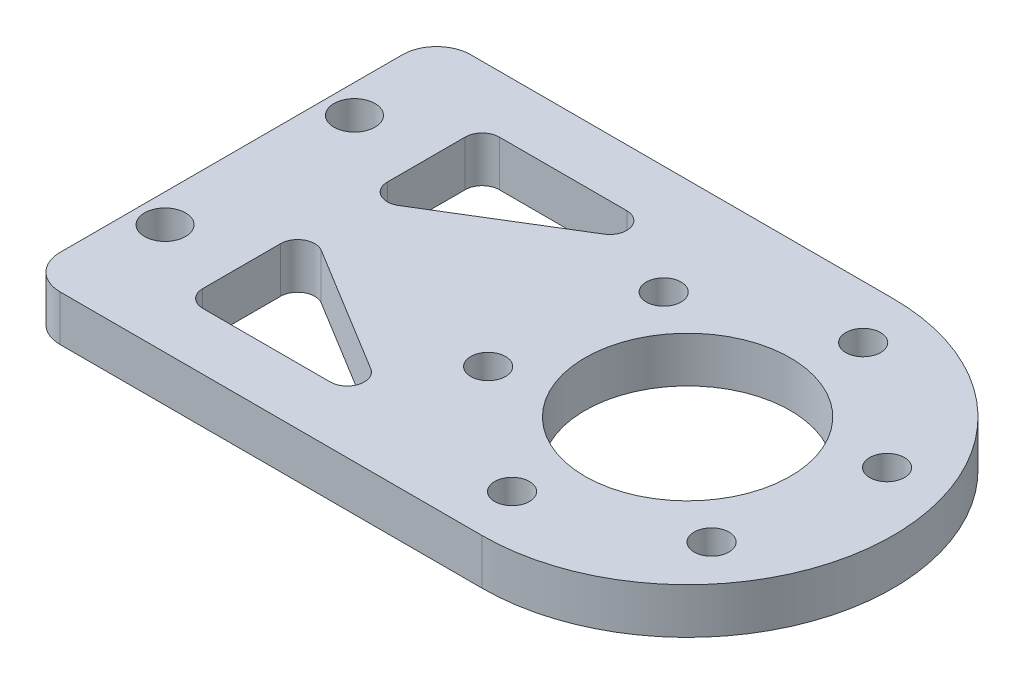
SolidWorks part; units mm, degrees
material "Thornel Mat VMA"
ref_plane "前视基准面" through (0, 0, 0) normal (0, 0, 1) x (1, 0, 0)
ref_plane "上视基准面" through (0, 0, 0) normal (0, 1, 0) x (1, 0, 0)
ref_plane "右视基准面" through (0, 0, 0) normal (1, 0, 0) x (0, 0, -1)
other "Configuration Table"
sketch "草图1" plane through (0, 0, 0) normal (0, 1, 0) x (1, 0, 0)
  line L1 (-20, -18) -> (20, -18)
  line L2 (-20, -18) -> (-20, 18)
  line L3 (-20, 18) -> (20, 18)
  line L4 (20, -18) -> (20, 18)
  line L5 (-20, -18) -> (20, 18) construction
  line L6 (-20, 18) -> (20, -18) construction
  circle A0 centre (20, 0) radius 18
  point P0 (0, 0)
  dimension "D1" = 36
  dimension "D2" = 40
extrude "凸台-拉伸1" add sketch "草图1" along normal blind 4 contours A0 L3 L2 L1 | L4 A0 | L4 A0
sketch "草图2" plane through (0, 4, 0) normal (0, 1, 0) x (1, 0, 0)
  circle A0 centre (9.4633, 8.4396) radius 1.525 construction
  circle A1 centre (7.4227, -4.9053) radius 1.525 construction
  circle A2 centre (30.5367, -8.4396) radius 1.525 construction
  circle A3 centre (17.9595, -13.3449) radius 1.525 construction
  circle A4 centre (32.5773, 4.9053) radius 1.525 construction
  circle A5 centre (22.0405, 13.3449) radius 1.525 construction
  circle A6 centre (9.4633, 8.4396) radius 1.525
  circle A7 centre (7.4227, -4.9053) radius 1.525
  circle A8 centre (30.5367, -8.4396) radius 1.525
  circle A9 centre (17.9595, -13.3449) radius 1.525
  circle A10 centre (32.5773, 4.9053) radius 1.525
  circle A11 centre (22.0405, 13.3449) radius 1.525
extrude "切除-拉伸1" cut sketch "草图2" against normal through all
sketch "草图3" plane through (0, 4, 0) normal (0, 1, 0) x (1, 0, 0)
  circle A0 centre (-17.5, -8.3) radius 1.25 construction
  circle A1 centre (-17.5, 8.3) radius 1.25 construction
  circle A2 centre (-17.5, -8.3) radius 1.25 construction
  circle A3 centre (-17.5, 8.3) radius 1.25 construction
  circle A4 centre (-17.5, -8.3) radius 1.8
  circle A5 centre (-17.5, 8.3) radius 1.8
  dimension "D1" = 0.55
fillet "圆角1" radius 3 2 edges at (-20, 2, -18) (-20, 2, 18)
extrude "切除-拉伸5" cut sketch "草图3" against normal through all
sketch "草图4" plane through (0, 4, 0) normal (0, 1, 0) x (1, 0, 0)
  line L0 (0, 0) -> (50000, 0) construction
  line L1 (-17, 18) -> (20, 18) construction
  line L2 (-11, 2) -> (7, 2)
  line L3 (-11, 2) -> (-11, 13)
  line L4 (-11, 13) -> (7, 13)
  line L5 (7, 2) -> (7, 13)
  line L6 (-11, 2) -> (7, 13) construction
  line L7 (-11, 13) -> (7, 2) construction
  line L8 (-20, -15) -> (-20, 15) construction
  line L9 (-11, 2) -> (7, 13)
  point P3 (-2, 7.5)
  dimension "D1" = 5
  dimension "D2" = 9
  dimension "D3" = 2
  dimension "D4" = 18
extrude "切除-拉伸3" cut sketch "草图4" against normal through all contours L3 L9 L4
fillet "圆角2" radius 1.5 3 edges at (7, 2, -13) (-11, 2, -2) (-11, 2, -13)
mirror "镜向1" about plane through (0, 0, 0) normal (0, 0, 1) of "圆角2", "切除-拉伸3"
sketch "草图5" plane through (0, 4, 0) normal (0, 1, 0) x (1, 0, 0)
  circle A0 centre (20, 0) radius 9
  arc A1 (20, -18) -> (20, 18) centre (20, 0) ccw construction
  dimension "D1" = 18
extrude "切除-拉伸4" cut sketch "草图5" against normal through all
